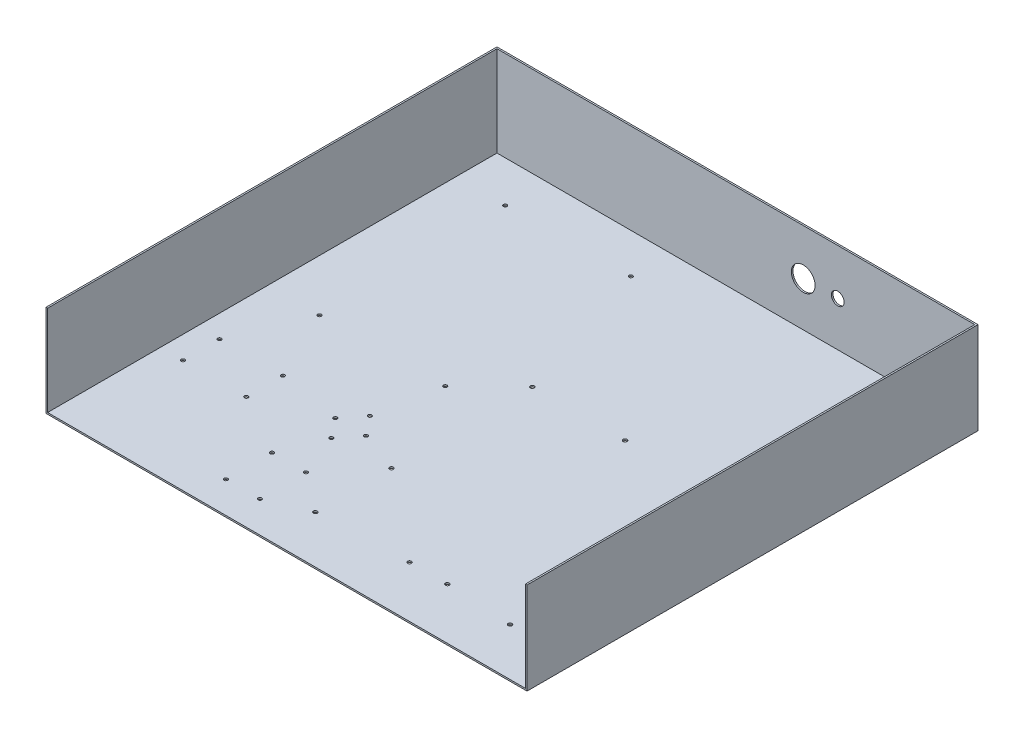
SolidWorks part; units mm, degrees
ref_plane "Front Plane" through (0, 0, 0) normal (0, 0, 1) x (1, 0, 0)
ref_plane "Top Plane" through (0, 0, 0) normal (0, 1, 0) x (1, 0, 0)
ref_plane "Right Plane" through (0, 0, 0) normal (1, 0, 0) x (0, 0, -1)
sketch "Sketch1" plane through (0, 0, 0) normal (0, 1, 0) x (1, 0, 0)
  line L1 (-215.9, 203.2) -> (215.9, 203.2)
  line L2 (-215.9, 203.2) -> (-215.9, -203.2)
  line L3 (-215.9, -203.2) -> (215.9, -203.2)
  line L4 (215.9, 203.2) -> (215.9, -203.2)
  line L5 (-215.9, 203.2) -> (215.9, -203.2) construction
  line L6 (-215.9, -203.2) -> (215.9, 203.2) construction
  point P0 (0, 0)
  dimension "D1" = 406.4
  dimension "D2" = 431.8
extrude "Boss-Extrude1" add sketch "Sketch1" along normal blind 82.55
shell "Shell1" thickness 1.4351
sketch "Sketch2" plane through (0, 0, 203.2) normal (0, 0, 1) x (1, 0, 0)
  line L1 (-215.9, 82.55) -> (215.9, 82.55)
  line L2 (-215.9, 82.55) -> (-215.9, 0)
  line L3 (-215.9, 0) -> (215.9, 0)
  line L4 (215.9, 82.55) -> (215.9, 0)
extrude "Cut-Extrude1" cut sketch "Sketch2" against normal blind 1.5875
sketch "Sketch4" plane through (0, 1.4351, 0) normal (0, 1, 0) x (1, 0, 0)
  line L0 (-214.4649, 201.7649) -> (-214.4649, -201.6125) construction
  line L1 (-214.4649, -201.6125) -> (214.4649, -201.6125) construction
  circle A4 centre (-170.0149, 164.6656) radius 1.632
  circle A5 centre (-58.517, 166.012) radius 1.632
  circle A6 centre (-167.9785, -3.9781) radius 1.632
  circle A7 centre (-56.4806, -2.6317) radius 1.6319
  dimension "D5" = 157.9843
  dimension "D7" = 198.9808
  dimension "D8" = 366.2781
  dimension "D9" = 367.6245
  dimension "D1" = 3.2639
  dimension "D2" = 44.45
  dimension "D3" = 46.4864
  dimension "D4" = 155.9479
  dimension "D6" = 197.6344
extrude "Cut-Extrude3" cut sketch "Sketch4" against normal blind 160.02
sketch "Sketch8" plane through (0, 0, -203.2) normal (0, 0, -1) x (-1, 0, 0)
  line L0 (215.9, 82.55) -> (215.9, 0) construction
  line L8 (-215.9, 0) -> (215.9, 0) construction
  circle A2 centre (-60.4636, 41.275) radius 10.668
  circle A3 centre (-91.445, 41.275) radius 5.715
  dimension "D1" = 11.43
  dimension "D4" = 307.345
  dimension "D2" = 21.336
  dimension "D3" = 276.3636
  dimension "D5" = 41.275
extrude "Cut-Extrude7" cut sketch "Sketch8" against normal through all
sketch "Sketch9" plane through (0, 1.4351, 0) normal (0, 1, 0) x (1, 0, 0)
  circle A8 centre (-52.007, -132.1613) radius 1.6319
  circle A13 centre (-52.007, -173.5189) radius 1.632
  circle A14 centre (-82.5251, -173.5189) radius 1.632
  circle A15 centre (-82.5251, -132.1613) radius 1.7145
  circle A16 centre (-137.4737, -100.2351) radius 1.632
  circle A17 centre (-194.2427, -100.2351) radius 1.632
  circle A18 centre (-137.4737, -67.431) radius 1.632
  circle A19 centre (-194.2427, -67.431) radius 1.632
  circle A20 centre (-56.4806, -2.6317) radius 1.6319 construction
  point P0 (-52.007, -173.5189)
  dimension "D2" = 3.2639
  dimension "D3" = 4.4736
  dimension "D4" = 26.0445
  dimension "D5" = 80.9931
  dimension "D6" = 137.7621
  dimension "D10" = 170.8872
  dimension "D1" = 3.429
  dimension "D7" = 64.7993
  dimension "D8" = 97.6034
  dimension "D9" = 129.5296
extrude "Cut-Extrude8" cut sketch "Sketch9" against normal blind 2.54
sketch "Sketch3" plane through (0, 1.4351, 0) normal (0, 1, 0) x (1, 0, 0)
  circle A0 centre (157.9346, 35.85) radius 1.75
  circle A1 centre (157.9346, -44.65) radius 1.75
  circle A2 centre (157.9346, -158.9) radius 1.75
  circle A3 centre (98.4346, -155.65) radius 1.75
  circle A4 centre (64.4446, -155.65) radius 1.75
  circle A5 centre (-16.8154, -158.9) radius 1.75
  circle A6 centre (66.4346, 35.85) radius 1.75
  circle A7 centre (-16.8154, 35.85) radius 1.75
  circle A8 centre (-16.8154, -90.65) radius 1.75
  circle A10 centre (-52.007, -132.1613) radius 1.6319 construction
  dimension "D5" = 150.4416
  dimension "D7" = 41.5113
  dimension "D6" = 209.9416
  dimension "D10" = 23.4887
  dimension "D11" = 26.7387
  dimension "D9" = 168.0113
  dimension "D3" = 116.4516
  dimension "D8" = 87.5113
  dimension "D1" = 3.5
  dimension "D2" = 35.1916
  dimension "D4" = 118.4416
extrude "Cut-Extrude2" cut sketch "Sketch3" against normal blind 160.02
sketch "Sketch5" plane through (0, 1.4351, 0) normal (0, 1, 0) x (1, 0, 0)
  circle A5 centre (-67.2489, -59.5859) radius 1.632
  circle A6 centre (-67.2489, -94.1299) radius 1.632
  circle A7 centre (-80.9649, -76.8579) radius 1.632
  circle A8 centre (-53.5329, -76.8579) radius 1.632
  circle A9 centre (-52.007, -173.5189) radius 1.6319 construction
  dimension "D4" = 28.9578
  dimension "D5" = 79.389
  dimension "D6" = 96.661
  dimension "D7" = 113.933
  dimension "D1" = 3.2639
  dimension "D2" = 1.5258
  dimension "D3" = 15.2418
extrude "Cut-Extrude6" cut sketch "Sketch5" against normal through all
